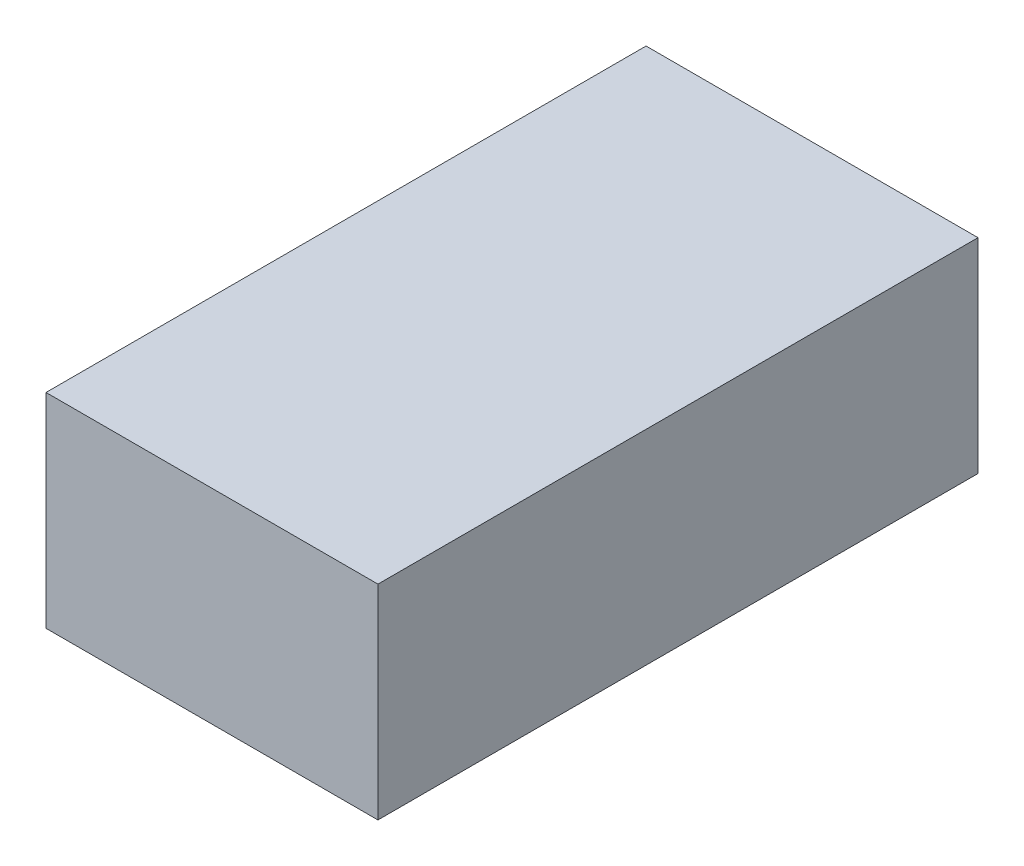
SolidWorks part; units mm, degrees
ref_plane "Plan de face" through (0, 0, 0) normal (0, 0, 1) x (1, 0, 0)
ref_plane "Plan de dessus" through (0, 0, 0) normal (0, 1, 0) x (1, 0, 0)
ref_plane "Plan de droite" through (0, 0, 0) normal (1, 0, 0) x (0, 0, -1)
sketch "Esquisse1" plane through (0, 0, 0) normal (0, 0, 1) x (1, 0, 0)
  line L1 (0, 0) -> (26, 0)
  line L2 (0, 0) -> (0, 16)
  line L3 (0, 16) -> (26, 16)
  line L4 (26, 0) -> (26, 16)
  dimension "D1" = 16
  dimension "D2" = 26
extrude "Boss.-Extru.1" add sketch "Esquisse1" along normal blind 47
